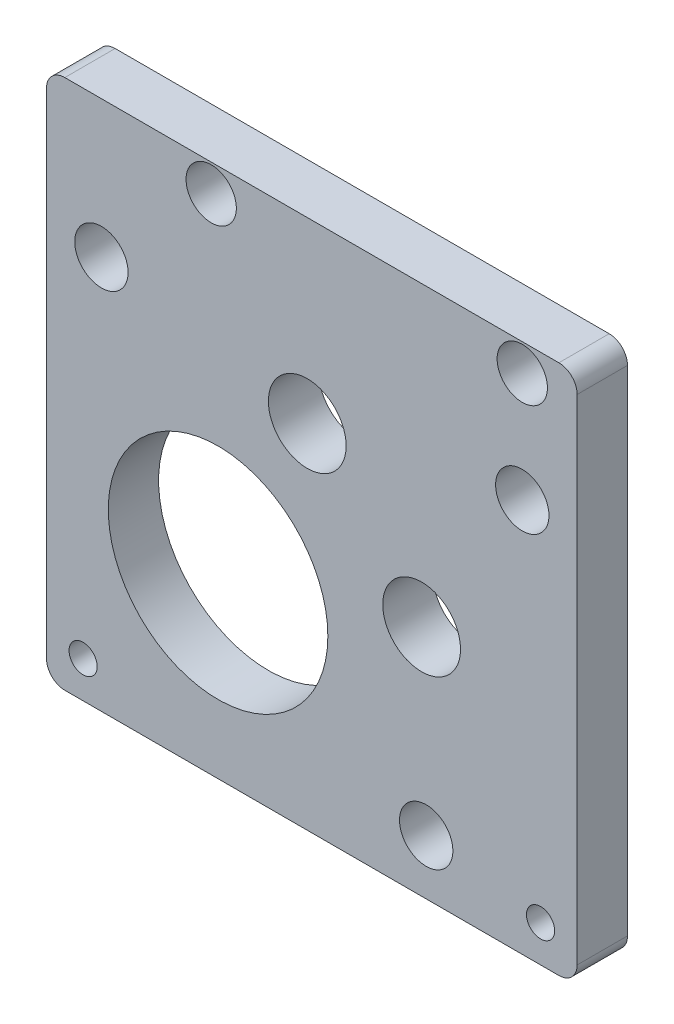
SolidWorks part; units mm, degrees
ref_plane "Front Plane" through (0, 0, 0) normal (0, 0, 1) x (1, 0, 0)
ref_plane "Top Plane" through (0, 0, 0) normal (0, 1, 0) x (1, 0, 0)
ref_plane "Right Plane" through (0, 0, 0) normal (1, 0, 0) x (0, 0, -1)
sketch "Sketch1" plane through (0, 0, 0) normal (0, 0, 1) x (1, 0, 0)
  line L0 (-29, 27) -> (-29, -27)
  line L1 (-27, -29) -> (27, -29)
  line L2 (29, -27) -> (29, 27)
  line L3 (27, 29) -> (-27, 29)
  circle A0 centre (-0.5, 9.5) radius 4.25
  circle A1 centre (25, -25) radius 1.5377
  circle A2 centre (12.5, -23) radius 2.916
  circle A3 centre (-11, 26) radius 2.75
  circle A4 centre (-10.25, -9.5) radius 12
  circle A5 centre (23, 26) radius 2.75
  circle A6 centre (23, 14) radius 2.916
  circle A7 centre (-23, 14) radius 2.916
  circle A8 centre (-25, -25) radius 1.5378
  circle A9 centre (12, -3.5) radius 4.25
  circle A10 centre (12, -3.5) radius 3.75
  circle A11 centre (-0.5, 9.5) radius 3.75
  arc A12 (-27, 29) -> (-29, 27) centre (-27, 27) ccw
  arc A13 (-29, -27) -> (-27, -29) centre (-27, -27) ccw
  arc A14 (27, -29) -> (29, -27) centre (27, -27) ccw
  arc A15 (29, 27) -> (27, 29) centre (27, 27) ccw
  dimension "D1" = 2
  dimension "D2" = 29
  dimension "D3" = 29
  dimension "D4" = 29
extrude "Boss-Extrude1" add sketch "Sketch1" along normal blind 5.5 contours L2 A15 L3 A12 L0 A13 L1 A14 A0 A1 A2 A3 A4 A5 A6 A7 A8 A9
